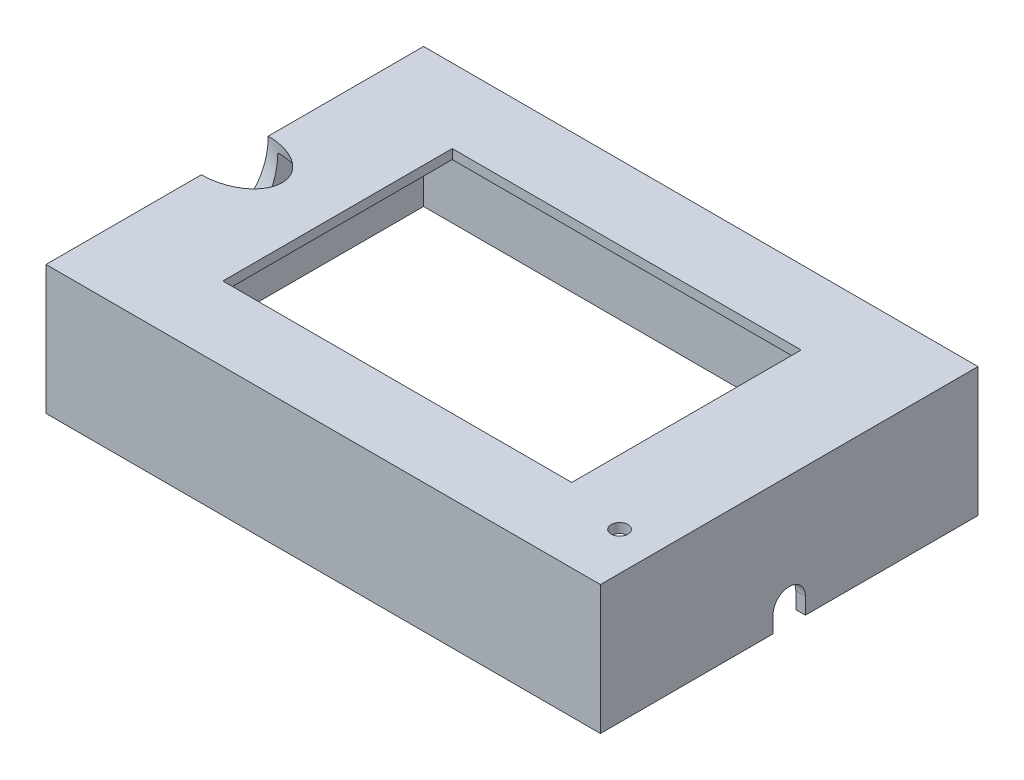
SolidWorks part; units mm, degrees
ref_plane "Front Plane" through (0, 0, 0) normal (0, 0, 1) x (1, 0, 0)
ref_plane "Top Plane" through (0, 0, 0) normal (0, 1, 0) x (1, 0, 0)
ref_plane "Right Plane" through (0, 0, 0) normal (1, 0, 0) x (0, 0, -1)
sketch "Sketch1" plane through (0, 0, 0) normal (0, 1, 0) x (1, 0, 0)
  line L0 (58, 39.5) -> (-58, 39.5)
  line L1 (56, -37.5) -> (-56, -37.5)
  line L2 (56, -37.5) -> (56, 37.5)
  line L3 (56, 37.5) -> (-56, 37.5)
  line L4 (-56, -37.5) -> (-56, 37.5)
  line L5 (56, -37.5) -> (-56, 37.5) construction
  line L6 (56, 37.5) -> (-56, -37.5) construction
  line L7 (-58, -39.5) -> (-58, 39.5)
  line L8 (58, -39.5) -> (-58, -39.5)
  line L9 (58, -39.5) -> (58, 39.5)
  point P0 (0, 0)
  dimension "D1" = 112
  dimension "D2" = 75
  dimension "D3" = 2
extrude "Boss-Extrude1" add sketch "Sketch1" along normal blind 25
sketch "Sketch2" plane through (0, 25, 0) normal (0, 1, 0) x (1, 0, 0)
  line L1 (58, -39.5) -> (-58, -39.5)
  line L2 (58, -39.5) -> (58, 39.5)
  line L3 (58, 39.5) -> (-58, 39.5)
  line L4 (-58, -39.5) -> (-58, 39.5)
  line L5 (58, -39.5) -> (-58, 39.5) construction
  line L6 (58, 39.5) -> (-58, -39.5) construction
  point P0 (0, 0)
extrude "Boss-Extrude2" add sketch "Sketch2" along normal blind 2
sketch "Sketch3" plane through (0, 27, 0) normal (0, 1, 0) x (1, 0, 0)
  line L1 (-36.5, 24) -> (36.5, 24)
  line L2 (-36.5, 24) -> (-36.5, -24)
  line L3 (-36.5, -24) -> (36.5, -24)
  line L4 (36.5, 24) -> (36.5, -24)
  line L5 (-36.5, 24) -> (36.5, -24) construction
  line L6 (-36.5, -24) -> (36.5, 24) construction
  point P0 (0, 0)
  dimension "D1" = 48
  dimension "D2" = 73
extrude "Cut-Extrude1" cut sketch "Sketch3" against normal up to surface (2 mm away) up to face at (0, 25, 0)
sketch "Sketch4" plane through (0, 27, 0) normal (0, 1, 0) x (1, 0, 0)
  line L0 (-58, -39.5) -> (58, -39.5) construction
  line L1 (58, -39.5) -> (58, 39.5) construction
  circle A0 centre (50, -27.5) radius 1.75
  dimension "D1" = 3.5
  dimension "D2" = 12
  dimension "D3" = 8
extrude "Cut-Extrude2" cut sketch "Sketch4" against normal up to surface (2 mm away) up to face at (0, 25, 0)
sketch "Sketch5" plane through (0, 0, 0) normal (0, -1, 0) x (1, 0, 0)
  line L0 (-58, -0.8295) -> (-85, -0.8295) construction
  line L1 (-58, -39.5) -> (-58, 39.5) construction
  dimension "D1" = 27
ref_plane "Plane1" through (-42.5, 42.5, 0) normal (0.7071, -0.7071, 0) x (-0.7071, -0.7071, 0)
sketch "Sketch6" plane through (-42.5, 42.5, 0) normal (0.7071, -0.7071, 0) x (-0.7071, -0.7071, 0)
  line L0 (21.9203, 39.5) -> (21.9203, -39.5) construction
  circle A0 centre (21.9203, 0) radius 7
  dimension "D1" = 14
extrude "Cut-Extrude3" cut sketch "Sketch6" along normal blind 10
sketch "Sketch7" plane through (58, 0, 0) normal (1, 0, 0) x (0, 0, -1)
  line L1 (0, 3.5) -> (0, 0) construction
  line L2 (-39.5, 0) -> (39.5, 0) construction
  line L3 (-3.375, 3.5) -> (-3.375, 0)
  line L4 (3.375, 3.5) -> (3.375, 0)
  line L5 (3.375, 0) -> (-3.375, 0)
  arc A0 (3.375, 3.5) -> (-3.375, 3.5) centre (0, 3.5) ccw
  dimension "D1" = 6.75
  dimension "D2" = 3.5
extrude "Cut-Extrude4" cut sketch "Sketch7" against normal up to surface (2 mm away) up to face at (56, 12.5, 0)
